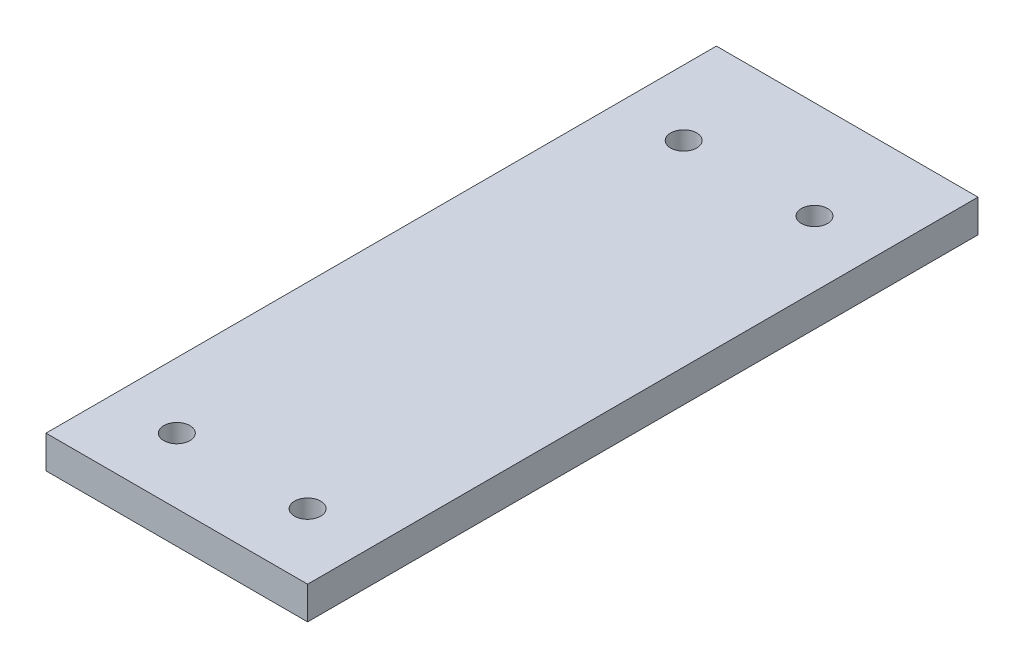
SolidWorks part; units mm, degrees
ref_plane "Front Plane" through (0, 0, 0) normal (0, 0, 1) x (1, 0, 0)
ref_plane "Top Plane" through (0, 0, 0) normal (0, 1, 0) x (1, 0, 0)
ref_plane "Right Plane" through (0, 0, 0) normal (1, 0, 0) x (0, 0, -1)
sketch "Sketch1" plane through (0, 0, 0) normal (0, 1, 0) x (1, 0, 0)
  line L1 (-49.4304, 151.2838) -> (30.5696, 151.2838)
  line L2 (-49.4304, 151.2838) -> (-49.4304, -53.7162)
  line L3 (-49.4304, -53.7162) -> (30.5696, -53.7162)
  line L4 (30.5696, 151.2838) -> (30.5696, -53.7162)
  dimension "D1" = 205
  dimension "D2" = 80
extrude "Boss-Extrude1" add sketch "Sketch1" along normal blind 10
sketch "Sketch2" plane through (0, 0, 0) normal (0, -1, 0) x (-1, 0, 0)
  line L0 (49.4304, -53.7162) -> (-30.5696, -53.7162) construction
  line L1 (49.4304, 151.2838) -> (49.4304, -53.7162) construction
  line L2 (-30.5696, -53.7162) -> (-30.5696, 151.2838) construction
  circle A0 centre (29.4304, -33.7162) radius 4
  circle A1 centre (-10.5696, -33.7162) radius 4
  point P4 (0, 0)
  dimension "D1" = 20
  dimension "D2" = 20
  dimension "D3" = 20
  dimension "D4" = 20
extrude "Cut-Extrude1" cut sketch "Sketch2" against normal blind 10
sketch "Sketch3" plane through (0, 0, 0) normal (0, -1, 0) x (-1, 0, 0)
  line L0 (-30.5696, 151.2838) -> (49.4304, 151.2838) construction
  line L1 (49.4304, 151.2838) -> (49.4304, -53.7162) construction
  line L2 (-30.5696, -53.7162) -> (-30.5696, 151.2838) construction
  circle A0 centre (29.4304, 121.2838) radius 4
  circle A1 centre (-10.5696, 121.2838) radius 4
  dimension "D1" = 30
  dimension "D2" = 20
  dimension "D3" = 30
  dimension "D4" = 20
extrude "Cut-Extrude2" cut sketch "Sketch3" against normal blind 10
sketch "Sketch4" plane through (0, 0, 0) normal (0, -1, 0) x (1, 0, 0)
  text T0 "Motor side"
  text T1 "Front"
extrude "Boss-Extrude3" add sketch "Sketch4" along normal blind 1
